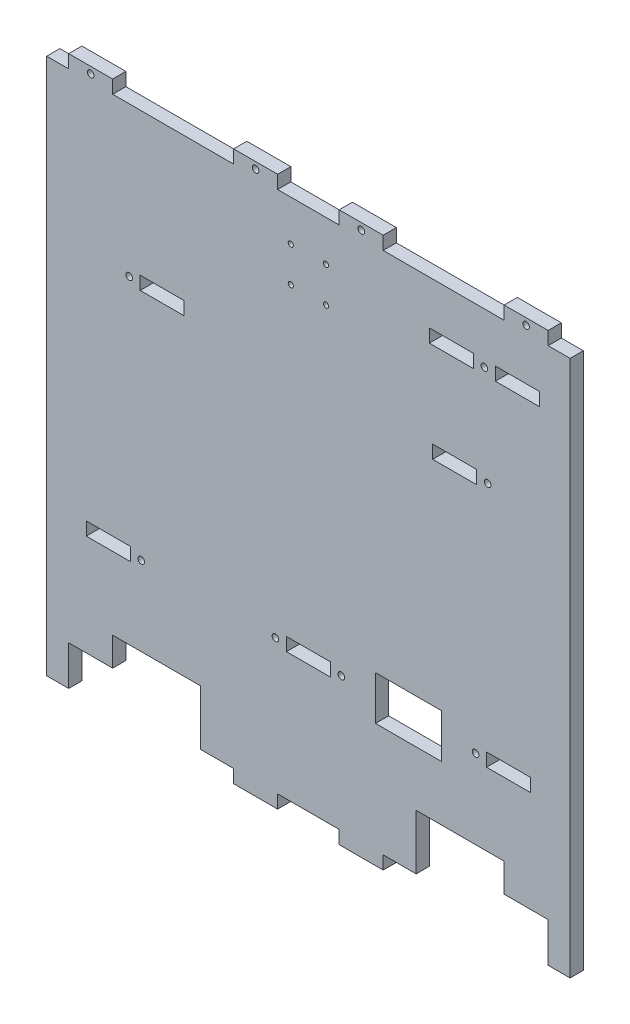
SolidWorks part; units mm, degrees
ref_plane "Plan de face" through (0, 0, 0) normal (0, 0, 1) x (1, 0, 0)
ref_plane "Plan de dessus" through (0, 0, 0) normal (0, 1, 0) x (1, 0, 0)
ref_plane "Plan de droite" through (0, 0, 0) normal (1, 0, 0) x (0, 0, -1)
sketch "Esquisse1" plane through (0, 0, 0) normal (0, 0, 1) x (1, 0, 0)
  line L0 (0, 139.6766) -> (0, -178.3461) construction
  line L1 (-109, 119) -> (109, 119)
  line L2 (-109, 119) -> (-109, -119)
  line L3 (-109, -119) -> (109, -119)
  line L4 (109, 119) -> (109, -119)
  line L5 (-101, -61) -> (-81, -61)
  line L6 (-101, -61) -> (-101, -55)
  line L7 (-101, -55) -> (-81, -55)
  line L8 (-81, -61) -> (-81, -55)
  line L9 (-10, -61) -> (10, -61)
  line L10 (-10, -61) -> (-10, -55)
  line L11 (-10, -55) -> (10, -55)
  line L12 (10, -61) -> (10, -55)
  line L13 (81, -61) -> (101, -61)
  line L14 (81, -61) -> (81, -55)
  line L15 (81, -55) -> (101, -55)
  line L16 (101, -61) -> (101, -55)
  line L17 (-76.5, 54) -> (-56.5, 54)
  line L18 (-76.5, 54) -> (-76.5, 48)
  line L19 (-76.5, 48) -> (-56.5, 48)
  line L20 (-56.5, 54) -> (-56.5, 48)
  line L21 (56.5, 54) -> (76.5, 54)
  line L22 (56.5, 54) -> (56.5, 48)
  line L23 (56.5, 48) -> (76.5, 48)
  line L24 (76.5, 54) -> (76.5, 48)
  line L25 (30.5, -69) -> (60.5, -69)
  line L26 (30.5, -69) -> (30.5, -49)
  line L27 (30.5, -49) -> (60.5, -49)
  line L28 (60.5, -69) -> (60.5, -49)
  line L30 (55, 99) -> (75, 99)
  line L31 (55, 99) -> (55, 93)
  line L32 (55, 93) -> (75, 93)
  line L33 (75, 99) -> (75, 93)
  line L34 (85, 99) -> (105, 99)
  line L35 (85, 99) -> (85, 93)
  line L36 (85, 93) -> (105, 93)
  line L37 (105, 99) -> (105, 93)
  dimension "D1" = 238
  dimension "D2" = 218
  dimension "D3" = 109
  dimension "D4" = 119
  dimension "D5" = 20
  dimension "D6" = 6
  dimension "D7" = 6
  dimension "D8" = 20
  dimension "D9" = 20
  dimension "D10" = 6
  dimension "D11" = 58
  dimension "D12" = 8
  dimension "D13" = 8
  dimension "D14" = 99
  dimension "D15" = 58
  dimension "D16" = 58
  dimension "D17" = 20
  dimension "D18" = 6
  dimension "D19" = 6
  dimension "D20" = 20
  dimension "D21" = 167
  dimension "D22" = 167
  dimension "D23" = 32.5
  dimension "D24" = 32.5
  dimension "D25" = 20
  dimension "D26" = 30
  dimension "D27" = 50
  dimension "D28" = 20.5
  dimension "D29" = 6
  dimension "D30" = 6
  dimension "D31" = 20
  dimension "D32" = 20
  dimension "D33" = 20
  dimension "D34" = 20
  dimension "D35" = 10
  dimension "D36" = 4
extrude "Boss.-Extru.1" add sketch "Esquisse1" along normal blind 6
sketch "Esquisse2" plane through (0, 0, 6) normal (0, 0, 1) x (1, 0, 0)
  line L0 (-109, -119) -> (109, -119) construction
  line L1 (-89, -119) -> (-49, -119)
  line L2 (-89, -119) -> (-89, -94)
  line L3 (-89, -94) -> (-49, -94)
  line L4 (-49, -119) -> (-49, -94)
  line L5 (-109, 119) -> (-109, -119) construction
  line L6 (49, -119) -> (89, -119)
  line L7 (49, -119) -> (49, -94)
  line L8 (49, -94) -> (89, -94)
  line L9 (89, -119) -> (89, -94)
  line L10 (109, -119) -> (109, 119) construction
  dimension "D1" = 40
  dimension "D2" = 20
  dimension "D3" = 40
  dimension "D4" = 20
  dimension "D5" = 25
  dimension "D6" = 25
extrude "Enlèv. mat.-Extru.1" cut sketch "Esquisse2" against normal blind 6
sketch "Esquisse3" plane through (0, 0, 6) normal (0, 0, 1) x (1, 0, 0)
  line L0 (0, 157.5653) -> (0, -190.6765) construction
  line L5 (-49, -119) -> (49, -119) construction
  line L6 (-34, -119) -> (-14, -119)
  line L7 (-34, -119) -> (-34, -125)
  line L8 (-34, -125) -> (-14, -125)
  line L9 (-14, -119) -> (-14, -125)
  line L10 (-49, -119) -> (-49, -94) construction
  line L15 (14, -119) -> (14, -125)
  line L16 (34, -125) -> (14, -125)
  line L17 (34, -119) -> (34, -125)
  line L18 (34, -119) -> (14, -119)
  line L19 (198.2674, 0) -> (-212.4835, 0) construction
  line L20 (0, -157.5653) -> (0, 190.6765) construction
  line L21 (34, 125) -> (14, 125)
  line L22 (14, 119) -> (14, 125)
  line L23 (89, 125) -> (109, 125)
  line L24 (89, 125) -> (89, 119)
  line L25 (89, 119) -> (109, 119)
  line L26 (109, 125) -> (109, 119)
  line L27 (-14, 119) -> (-14, 125)
  line L28 (-34, 125) -> (-14, 125)
  line L29 (-34, 119) -> (-34, 125)
  line L30 (-34, 119) -> (-14, 119)
  line L31 (-109, 125) -> (-109, 119)
  line L32 (-89, 119) -> (-109, 119)
  line L33 (-89, 125) -> (-89, 119)
  line L34 (-89, 125) -> (-109, 125)
  line L35 (34, 119) -> (14, 119)
  line L36 (34, 119) -> (34, 125)
  dimension "D2" = 20
  dimension "D3" = 6
  dimension "D4" = 15
extrude "Boss.-Extru.3" add sketch "Esquisse3" against normal blind 6
sketch "Esquisse4" plane through (0, 0, 6) normal (0, 0, 1) x (1, 0, 0)
  line L0 (-111.0944, 51) -> (126.4062, 51) construction
  line L1 (116.6655, -58) -> (-122.9189, -58) construction
  line L2 (76.5, 48) -> (76.5, 54) construction
  line L3 (0, 153.5677) -> (0, -173.1111) construction
  line L4 (45.0686, 96) -> (109.1297, 96) construction
  line L5 (81, -55) -> (81, -61) construction
  line L6 (10, -61) -> (10, -55) construction
  line L7 (-10, -55) -> (-10, -61) construction
  line L8 (75, 93) -> (75, 99) construction
  line L9 (-114.2336, 122) -> (-6.2018, 122) construction
  line L10 (-56.5, 54) -> (-76.5, 54) construction
  line L11 (-89, 125) -> (-109, 125) construction
  line L12 (-34, 125) -> (-34, 119) construction
  line L13 (55, 93) -> (75, 93) construction
  line L14 (-89, 119) -> (-89, 125) construction
  circle A0 centre (-15, -58) radius 1.5
  circle A1 centre (-76, -58) radius 1.5
  circle A2 centre (80, 96) radius 1.5
  circle A3 centre (81.5, 51) radius 1.5
  circle A4 centre (76, -58) radius 1.5
  circle A5 centre (15, -58) radius 1.5
  circle A6 centre (-81.5, 51) radius 1.5
  circle A7 centre (-99, 122) radius 1.5
  circle A8 centre (-24, 122) radius 1.5
  circle A9 centre (24, 122) radius 1.5
  circle A10 centre (99, 122) radius 1.5
  dimension "D2" = 5
  dimension "D3" = 3
  dimension "D4" = 3
  dimension "D5" = 5
  dimension "D6" = 5
  dimension "D7" = 3
  dimension "D8" = 3
  dimension "D9" = 3
  dimension "D10" = 5
  dimension "D11" = 3
  dimension "D12" = 5
  dimension "D13" = 3
  dimension "D15" = 3
  dimension "D16" = 3
  dimension "D17" = 10
  dimension "D18" = 10
  dimension "D14" = 3
extrude "Enlèv. mat.-Extru.2" cut sketch "Esquisse4" against normal blind 6
sketch "Esquisse5" plane through (0, 0, 6) normal (0, 0, 1) x (1, 0, 0)
  line L0 (-109, 119) -> (-109, -125)
  line L1 (-109, 119) -> (-119, 119)
  line L2 (-109, -125) -> (-119, -125)
  line L3 (-119, 119) -> (-119, -125)
  line L5 (109, -125) -> (109, 119)
  line L6 (109, -125) -> (119, -125)
  line L7 (109, 119) -> (119, 119)
  line L8 (119, -125) -> (119, 119)
  line L11 (109, 125) -> (89, 125) construction
  line L12 (-89, 125) -> (-109, 125) construction
  dimension "D1" = 10
  dimension "D2" = 10
  dimension "D3" = 244
  dimension "D4" = 244
  dimension "D5" = 6
  dimension "D6" = 6
extrude "Boss.-Extru.4" add sketch "Esquisse5" against normal blind 6
sketch "Esquisse6" plane through (0, 0, 6) normal (0, 0, 1) x (1, 0, 0)
  line L0 (0, 108.4917) -> (0, -172.5759) construction
  line L1 (89, -119) -> (109, -119)
  line L2 (89, -119) -> (89, -107)
  line L3 (89, -107) -> (109, -107)
  line L4 (109, -119) -> (109, -107)
  line L5 (-109, -119) -> (-109, -107)
  line L6 (-89, -107) -> (-109, -107)
  line L7 (-89, -119) -> (-89, -107)
  line L8 (-89, -119) -> (-109, -119)
  dimension "D1" = 12
  dimension "D2" = 20
extrude "Enlèv. mat.-Extru.3" cut sketch "Esquisse6" against normal blind 6
sketch "Esquisse7" plane through (0, 0, 6) normal (0, 0, 1) x (1, 0, 0)
  line L0 (14, 119) -> (-14, 119) construction
  line L1 (14, 125) -> (14, 119) construction
  circle A0 centre (-8, 100.5) radius 1.175
  circle A1 centre (8, 100.5) radius 1.175
  circle A2 centre (-8, 84.5) radius 1.175
  circle A3 centre (8, 84.5) radius 1.175
  dimension "D1" = 16
  dimension "D7" = 2.35
  dimension "D8" = 2.35
  dimension "D9" = 2.35
  dimension "D10" = 2.35
  dimension "D2" = 16
  dimension "D3" = 16
  dimension "D4" = 16
  dimension "D5" = 18.5
  dimension "D6" = 6
  dimension "D11" = 18.5
extrude "Enlèv. mat.-Extru.4" cut sketch "Esquisse7" against normal through all
equation "\"D3@Esquisse1\"=\"D2@Esquisse1\"/2"
equation "\"D4@Esquisse1\"=\"D1@Esquisse1\"/2"
